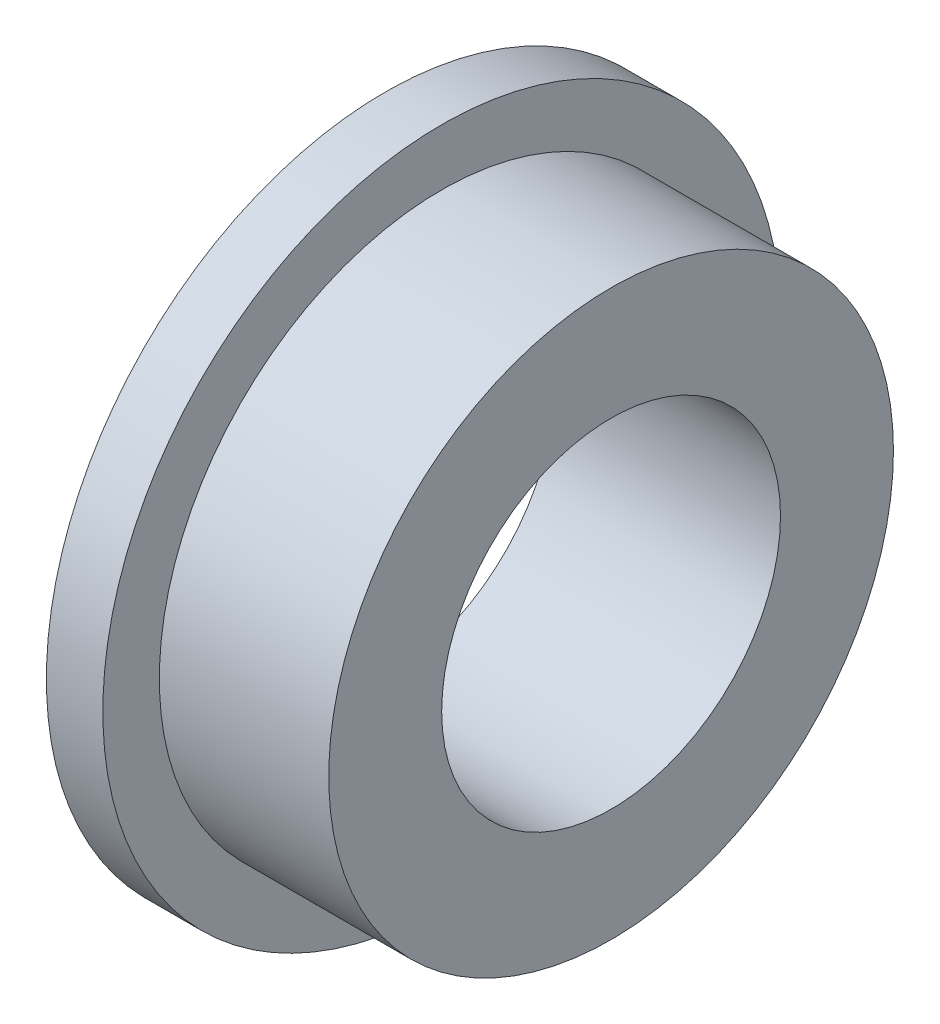
SolidWorks part; units mm, degrees
ref_plane "Front" through (0, 0, 0) normal (0, 0, 1) x (1, 0, 0)
ref_plane "Top" through (0, 0, 0) normal (0, 1, 0) x (1, 0, 0)
ref_plane "Right" through (0, 0, 0) normal (1, 0, 0) x (0, 0, -1)
sketch "草图1" plane through (0, 0, 0) normal (1, 0, 0) x (0, 0, -1)
  circle A0 centre (0, 0) radius 3
  circle A1 centre (0, 0) radius 6
  dimension "D1" = 6
  dimension "D2" = 12
extrude "凸台-拉伸1" add sketch "草图1" along normal blind 1
sketch "草图2" plane through (1, 0, 0) normal (1, 0, 0) x (0, 0, -1)
  circle A0 centre (0, 0) radius 3
  circle A1 centre (0, 0) radius 5
  dimension "D1" = 10
extrude "凸台-拉伸2" add sketch "草图2" along normal blind 3
